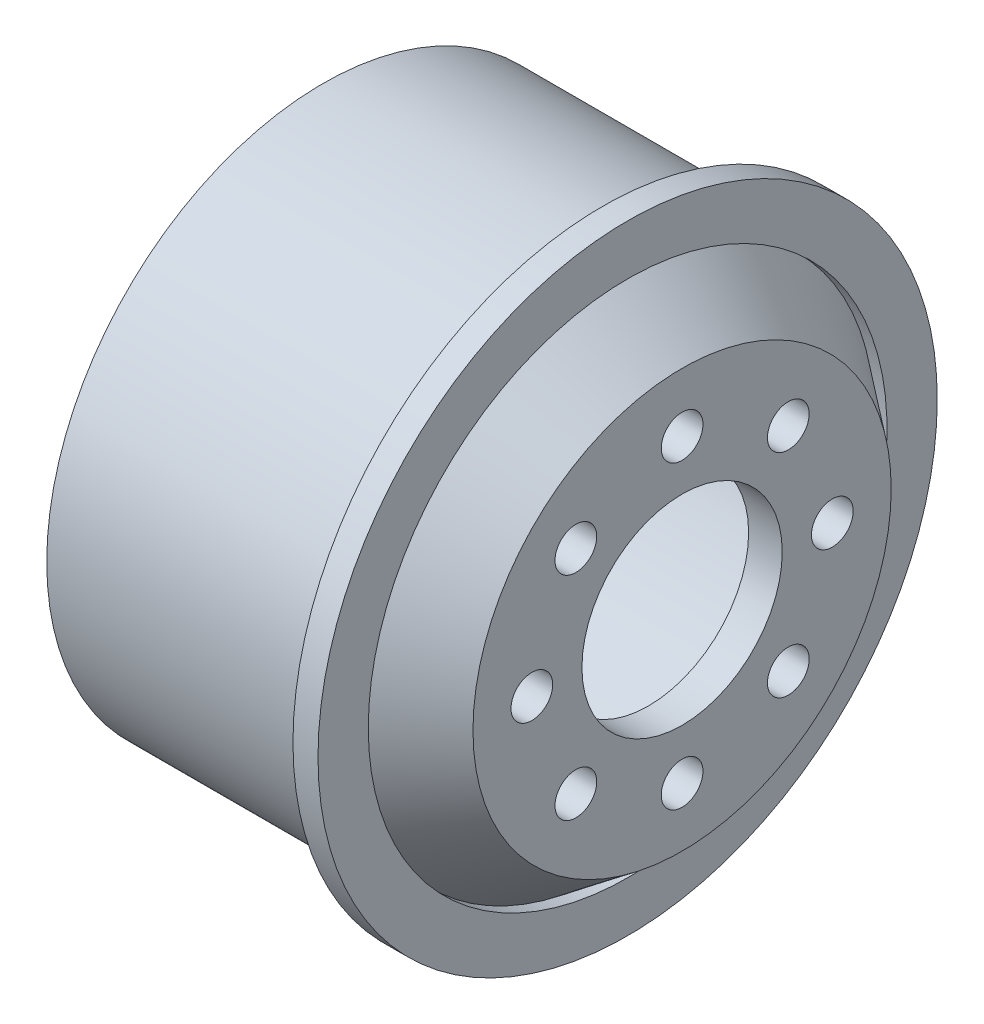
SolidWorks part; units mm, degrees
ref_plane "Front Plane" through (0, 0, 0) normal (0, 0, 1) x (1, 0, 0)
ref_plane "Top Plane" through (0, 0, 0) normal (0, 1, 0) x (1, 0, 0)
ref_plane "Right Plane" through (0, 0, 0) normal (1, 0, 0) x (0, 0, -1)
sketch "Sketch1" plane through (0, 0, 0) normal (0, 1, 0) x (1, 0, 0)
  line L0 (-37.2789, 0) -> (44.8184, 0) construction
  line L12 (-12.5637, 14.55) -> (-12.5637, 16.55)
  line L13 (-12.5637, 16.55) -> (4.1863, 16.55)
  line L18 (5.6863, 15.538) -> (4.9553, 15.538)
  line L23 (4.9553, 15.538) -> (8.9491, 12.5285)
  line L26 (-12.5637, 14.55) -> (2.9431, 14.55)
  line L27 (2.9431, 14.55) -> (6.9363, 11.5409)
  line L28 (4.1863, 16.55) -> (4.1863, 18.55)
  line L29 (4.1863, 18.55) -> (5.6863, 18.55)
  line L30 (5.6863, 18.55) -> (5.6863, 15.538)
  line L34 (6.9363, 11.5409) -> (6.9363, 6)
  line L35 (6.9363, 6) -> (8.9491, 6)
  line L37 (8.9491, 12.5285) -> (8.9491, 6)
  point P3 (8.936, 7.0891)
  point P4 (7.9363, 16.8502)
  point P5 (4.0798, 13.7427)
  point P16 (8.0798, 11.847)
  dimension "D1" = 29.1
  dimension "D2" = 12
  dimension "D4" = 2
  dimension "D5" = 2
  dimension "D6" = 1.5
  dimension "D7" = 143
  dimension "D12" = 33.1
  dimension "D3" = 5
  dimension "D15" = 19.5
  dimension "D19" = 23.0818
revolve "Revolve1" add sketch "Sketch1" angle 360 about L0
sketch "Sketch2" plane through (8.9491, 0, 0) normal (1, 0, 0) x (0, 0, -1)
  circle A0 centre (0, 0) radius 9 construction
  circle A1 centre (0, 9) radius 1.25
  circle A2 centre (6.364, 6.364) radius 1.25
  circle A3 centre (9, 0) radius 1.25
  circle A4 centre (6.364, -6.364) radius 1.25
  circle A5 centre (0, -9) radius 1.25
  circle A6 centre (-6.364, -6.364) radius 1.25
  circle A7 centre (-9, 0) radius 1.25
  circle A8 centre (-6.364, 6.364) radius 1.25
  point P22 (0, 0)
  dimension "D1" = 18
  dimension "D2" = 2.5
  dimension "D3" = 8
extrude "Cut-Extrude1" cut sketch "Sketch2" against normal through all
